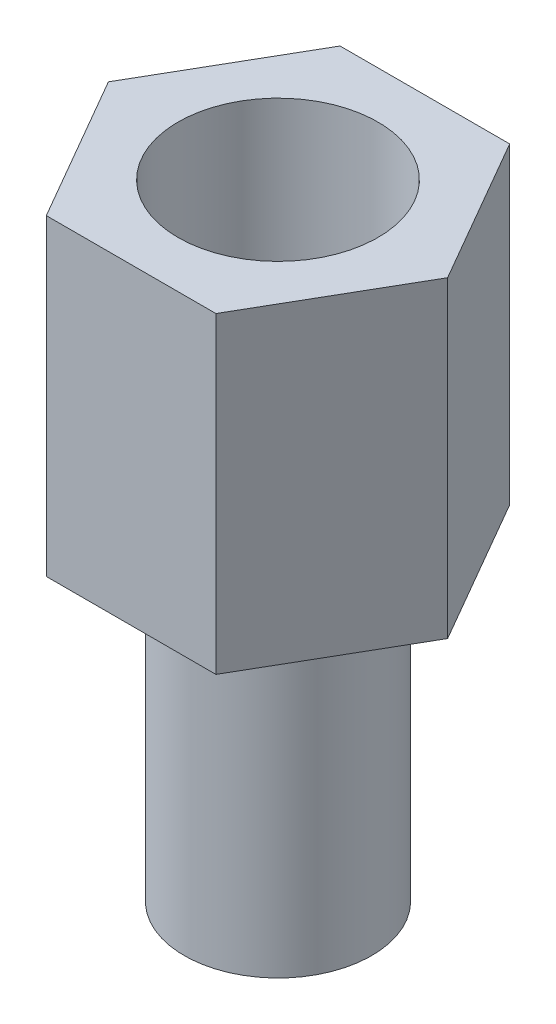
SolidWorks part; units mm, degrees
material "黄铜"
ref_plane "前视基准面" through (0, 0, 0) normal (0, 0, 1) x (1, 0, 0)
ref_plane "上视基准面" through (0, 0, 0) normal (0, 1, 0) x (1, 0, 0)
ref_plane "右视基准面" through (0, 0, 0) normal (1, 0, 0) x (0, 0, -1)
sketch "草图1" plane through (0, 0, 0) normal (0, 1, 0) x (1, 0, 0)
  line L1 (2.7135, 0) -> (1.3568, 2.35)
  line L2 (1.3568, 2.35) -> (-1.3568, 2.35)
  line L3 (-1.3568, 2.35) -> (-2.7135, 0)
  line L4 (-2.7135, 0) -> (-1.3568, -2.35)
  line L5 (-1.3568, -2.35) -> (1.3568, -2.35)
  line L6 (1.3568, -2.35) -> (2.7135, 0)
  circle A0 centre (0, 0) radius 2.35 construction
  dimension "D1" = 4.7
extrude "凸台-拉伸1" add sketch "草图1" along normal blind 5
sketch "草图2" plane through (0, 5, 0) normal (0, 1, 0) x (1, 0, 0)
  circle A0 centre (0, 0) radius 1.6
  dimension "D1" = 3.2
extrude "切除-拉伸1" cut sketch "草图2" against normal offset from surface (4 mm away) 1 up to face at (0, 0, 0)
sketch "草图3" plane through (0, 0, 0) normal (0, -1, 0) x (1, 0, 0)
  circle A0 centre (0, 0) radius 1.5
  dimension "D1" = 3
extrude "凸台-拉伸2" add sketch "草图3" along normal blind 5
